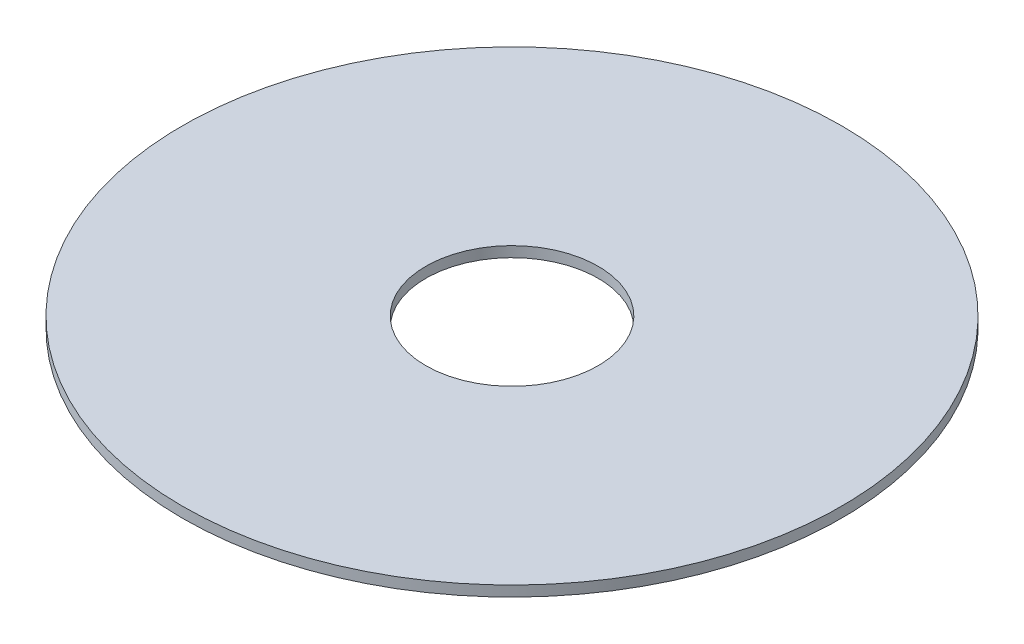
SolidWorks part; units mm, degrees
ref_plane "Front Plane" through (0, 0, 0) normal (0, 0, 1) x (1, 0, 0)
ref_plane "Top Plane" through (0, 0, 0) normal (0, 1, 0) x (1, 0, 0)
ref_plane "Right Plane" through (0, 0, 0) normal (1, 0, 0) x (0, 0, -1)
sketch "Sketch1" plane through (0, 0, 0) normal (0, 1, 0) x (1, 0, 0)
  circle A0 centre (0, 0) radius 53.5344
  circle A1 centre (0, 0) radius 14
extrude "Boss-Extrude1" add sketch "Sketch1" along normal blind 1.7
scale "Scale2" scale about centroid uniform scaling yes scale factor 0.75
